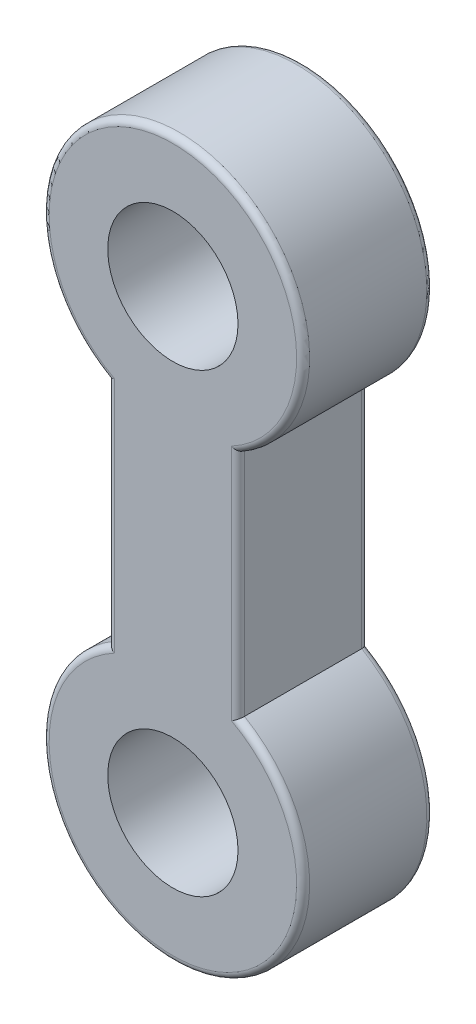
SolidWorks part; units mm, degrees
material "Plain Carbon Steel"
ref_plane "Plan de face" through (0, 0, 0) normal (0, 0, 1) x (1, 0, 0)
ref_plane "Plan de dessus" through (0, 0, 0) normal (0, 1, 0) x (1, 0, 0)
ref_plane "Plan de droite" through (0, 0, 0) normal (1, 0, 0) x (0, 0, -1)
sketch "Esquisse1" plane through (0, 0, 0) normal (0, 0, 1) x (1, 0, 0)
  line L1 (-10, -17.3205) -> (-10, -52.6795)
  line L2 (10, -17.3205) -> (10, -52.6795)
  circle A0 centre (0, 0) radius 10
  arc A1 (10, -17.3205) -> (-10, -17.3205) centre (0, 0) ccw
  circle A2 centre (0, -70) radius 10
  arc A3 (-10, -52.6795) -> (10, -52.6795) centre (0, -70) ccw
  point P7 (-10, 0)
  point P8 (-10, -70)
  point P9 (10, 0)
  point P10 (10, -70)
extrude "Boss.-Extru.1" add sketch "Esquisse1" along normal blind 20
fillet "Congé2" radius 1 8 edges at (0, -90, 20) (-10, -35, 20) (0, 20, 20) (10, -35, 20) (10, -35, 0) (0, -90, 0) (-10, -35, 0) (0, 20, 0)
sketch "Sketch1" plane through (0, 0, 20) normal (0, 0, 1) x (1, 0, 0)
  point P0 (0, 0)
  point P1 (0, -70)
sketch "Sketch2" plane through (0, 0, 0) normal (0, 0, -1) x (-1, 0, 0)
  point P0 (0, 0)
  point P1 (0, -70)
